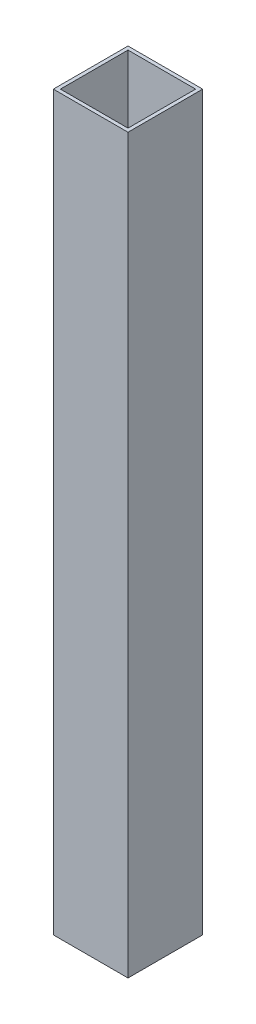
SolidWorks part; units mm, degrees
ref_plane "Alzado" through (0, 0, 0) normal (0, 0, 1) x (1, 0, 0)
ref_plane "Planta" through (0, 0, 0) normal (0, 1, 0) x (1, 0, 0)
ref_plane "Vista lateral" through (0, 0, 0) normal (1, 0, 0) x (0, 0, -1)
sketch "Sketch1" plane through (0, 0, 0) normal (0, 1, 0) x (1, 0, 0)
  line L0 (0, 0) -> (25.4, 0)
  line L1 (25.4, 0) -> (25.4, 25.4)
  line L2 (25.4, 25.4) -> (0, 25.4)
  line L3 (0, 25.4) -> (0, 0)
  line L4 (1.2, 24.2) -> (1.2, 1.2)
  line L5 (1.2, 1.2) -> (24.2, 1.2)
  line L6 (24.2, 1.2) -> (24.2, 24.2)
  line L7 (24.2, 24.2) -> (1.2, 24.2)
  dimension "D1" = 25.4
  dimension "D2" = 25.4
  dimension "D3" = 1.2
  dimension "D4" = 1.2
  dimension "D5" = 1.2
  dimension "D6" = 1.2
extrude "Boss-Extrude1" add sketch "Sketch1" along normal blind 249.2
